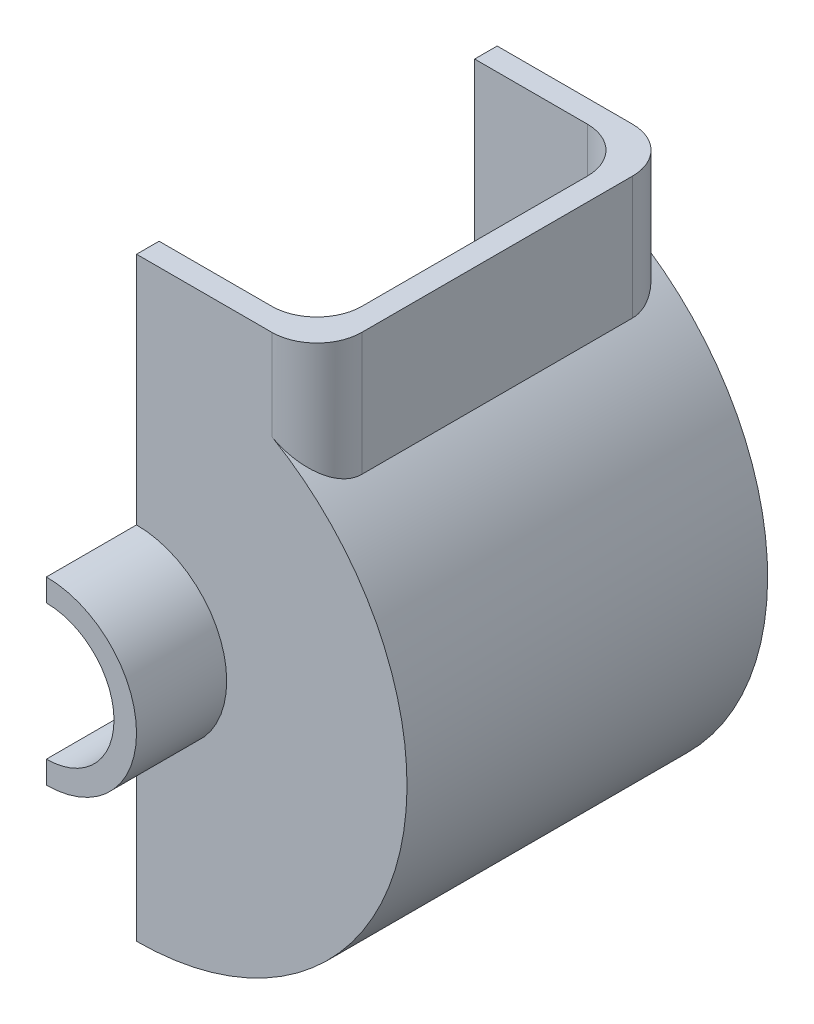
SolidWorks part; units mm, degrees
ref_plane "Front Plane" through (0, 0, 0) normal (0, 0, 1) x (1, 0, 0)
ref_plane "Top Plane" through (0, 0, 0) normal (0, 1, 0) x (1, 0, 0)
ref_plane "Right Plane" through (0, 0, 0) normal (1, 0, 0) x (0, 0, -1)
sketch "Sketch1" plane through (0, 0, 0) normal (0, 0, 1) x (1, 0, 0)
  line L0 (0, -20) -> (0, -15)
  line L1 (0, 15) -> (0, 20)
  arc A0 (0, -15) -> (0, 15) centre (0, 0) ccw
  arc A1 (0, -20) -> (0, 20) centre (0, 0) ccw
  dimension "D1" = 30
  dimension "D2" = 40
extrude "Boss-Extrude1" add sketch "Sketch1" along normal blind 25
sketch "Sketch3" plane through (0, 0, 0) normal (0, 0, 1) x (1, 0, 0)
  line L0 (0, -20) -> (0, -60)
  line L1 (0, 20) -> (0, 60)
  line L2 (40, 44.7214) -> (40, 72)
  line L3 (40, 72) -> (0, 72)
  line L4 (0, 72) -> (0, 60)
  arc A0 (0, -60) -> (40, 44.7214) centre (0, 0) ccw
  arc A1 (0, -20) -> (0, 20) centre (0, 0) ccw construction
  arc A2 (0, -20) -> (0, 20) centre (0, 0) ccw
  dimension "D1" = 120
  dimension "D2" = 52
  dimension "D3" = 40
extrude "Boss-Extrude3" add sketch "Sketch3" along normal blind 5 separate body
ref_plane "Plane2" through (0, 0, -35) normal (0, 0, 1) x (1, 0, 0)
mirror "Mirror5" about plane through (0, 0, -35) normal (0, 0, 1) of bodies 101 104
sketch "Sketch5" plane through (0, 0, 0) normal (0, 0, 1) x (1, 0, 0)
  line L0 (40, 44.7214) -> (40, 72) construction
  line L1 (40, 44.7214) -> (40, 72)
  arc A0 (0, -60) -> (40, 44.7214) centre (0, 0) ccw construction
  arc A1 (0, -60) -> (40, 44.7214) centre (0, 0) ccw
extrude "Extrude-Thin2" add sketch "Sketch5" against normal up to next thin
fillet "Fillet1" radius 10 4 edges at (40, 58.3607, 5) (40, 58.3607, -75) (35, 57.2132, 0) (35, 57.2132, -70)
